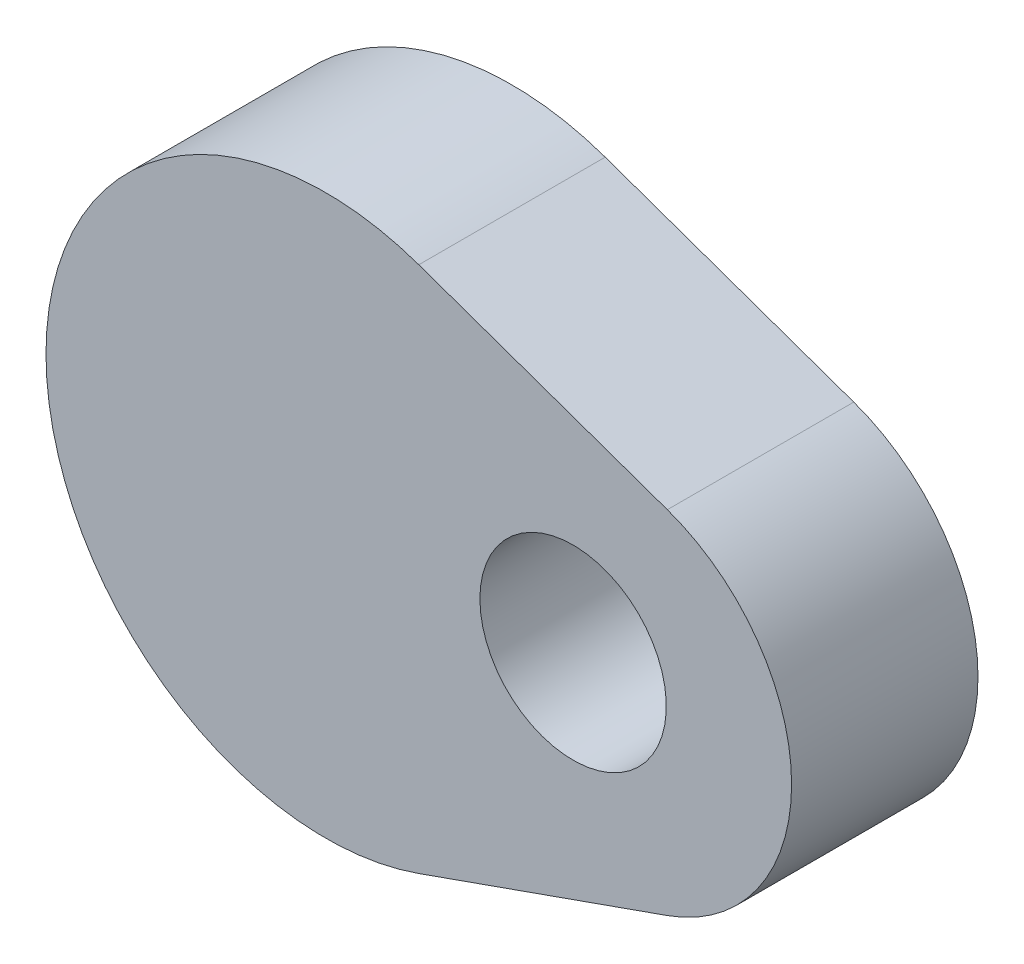
SolidWorks part; units mm, degrees
ref_plane "前视基准面" through (0, 0, 0) normal (0, 0, 1) x (1, 0, 0)
ref_plane "上视基准面" through (0, 0, 0) normal (0, 1, 0) x (1, 0, 0)
ref_plane "右视基准面" through (0, 0, 0) normal (1, 0, 0) x (0, 0, -1)
other "Configuration Table"
sketch "草图1" plane through (0, 0, 0) normal (0, 0, 1) x (1, 0, 0)
  line L0 (5, 14.1421) -> (18.3333, 9.4281)
  line L1 (18.3333, -9.4281) -> (5, -14.1421)
  line L2 (0, 0) -> (15, 0) construction
  arc A0 (5, 14.1421) -> (5, -14.1421) centre (0, 0) ccw
  arc A1 (18.3333, 9.4281) -> (18.3333, -9.4281) centre (15, 0) cw
  point P7 (0, 0)
  dimension "D1" = 15
  dimension "D2" = 10
  dimension "D3" = 15
extrude "凸台-拉伸1" add sketch "草图1" along normal blind 10
sketch "草图3" plane through (0, 0, 0) normal (0, 0, -1) x (-1, 0, 0)
  circle A0 centre (-13.2773, 0.2629) radius 5
  dimension "D1" = 10
extrude "切除-拉伸1" cut sketch "草图3" against normal through all
